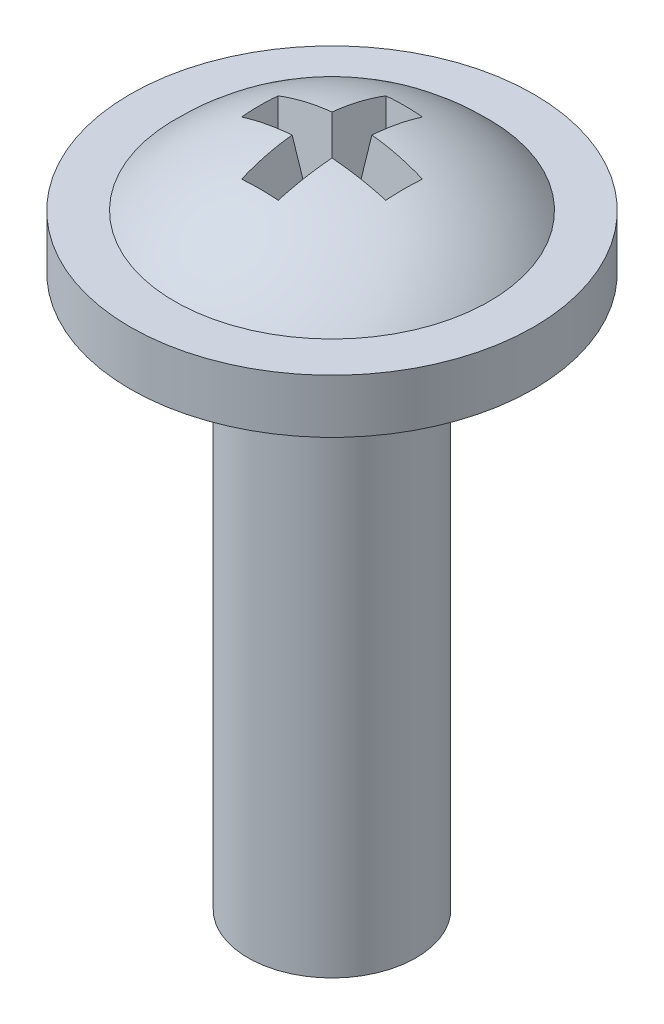
SolidWorks part; units mm, degrees
ref_plane "FRONT" through (0, 0, 0) normal (0, 0, 1) x (1, 0, 0)
ref_plane "TOP" through (0, 0, 0) normal (0, 1, 0) x (1, 0, 0)
ref_plane "SIDE" through (0, 0, 0) normal (1, 0, 0) x (0, 0, -1)
sketch "Sketch1" plane through (0, 0, 0) normal (0, 0, 1) x (1, 0, 0)
  line L0 (0, 0) -> (0, 12.7) construction
  line L1 (0, 0) -> (1.5875, 0)
  line L2 (1.5875, 0) -> (1.5875, 10.414)
  line L3 (1.5875, 10.414) -> (3.81, 10.414)
  line L4 (3.81, 10.414) -> (3.81, 11.43)
  line L5 (3.81, 11.43) -> (2.9718, 11.43)
  line L6 (0, 0) -> (0, 12.7)
  arc A0 (2.9718, 11.43) -> (0, 12.7) centre (0, 8.588) ccw
  dimension "D1" = 12.7
  dimension "D2" = 1.5875
  dimension "D3" = 10.414
  dimension "D4" = 3.81
  dimension "D5" = 1.016
  dimension "D6" = 2.9718
revolve "Base-Revolve" add sketch "Sketch1" angle 360 about L0
ref_plane "Plane1" through (0, 12.7, 0) normal (0, 1, 0) x (-1, 0, 0)
sketch "Sketch2" plane through (0, 12.7, 0) normal (0, 1, 0) x (-1, 0, 0)
  line L0 (0.381, 1.397) -> (-0.381, 1.397)
  line L1 (0.381, 1.397) -> (0.381, 0.381)
  line L2 (-0.381, -1.397) -> (0.381, -1.397)
  line L3 (-0.381, -1.397) -> (-0.381, -0.381)
  line L4 (1.397, 0.381) -> (0.381, 0.381)
  line L5 (1.397, 0.381) -> (1.397, -0.381)
  line L6 (-1.397, -0.381) -> (-0.381, -0.381)
  line L7 (-1.397, -0.381) -> (-1.397, 0.381)
  line L8 (0.381, -0.381) -> (1.397, -0.381)
  line L9 (0.381, -0.381) -> (0.381, -1.397)
  line L10 (-0.381, 0.381) -> (-0.381, 1.397)
  line L11 (-0.381, 0.381) -> (-1.397, 0.381)
  line L12 (-1.397, 0) -> (0, 0) construction
  line L13 (0, -1.397) -> (0, 0) construction
  dimension "D1" = 0.762
  dimension "D2" = 2.794
extrude "Cut-Extrude1" cut sketch "Sketch2" against normal blind 2.032 draft 8
